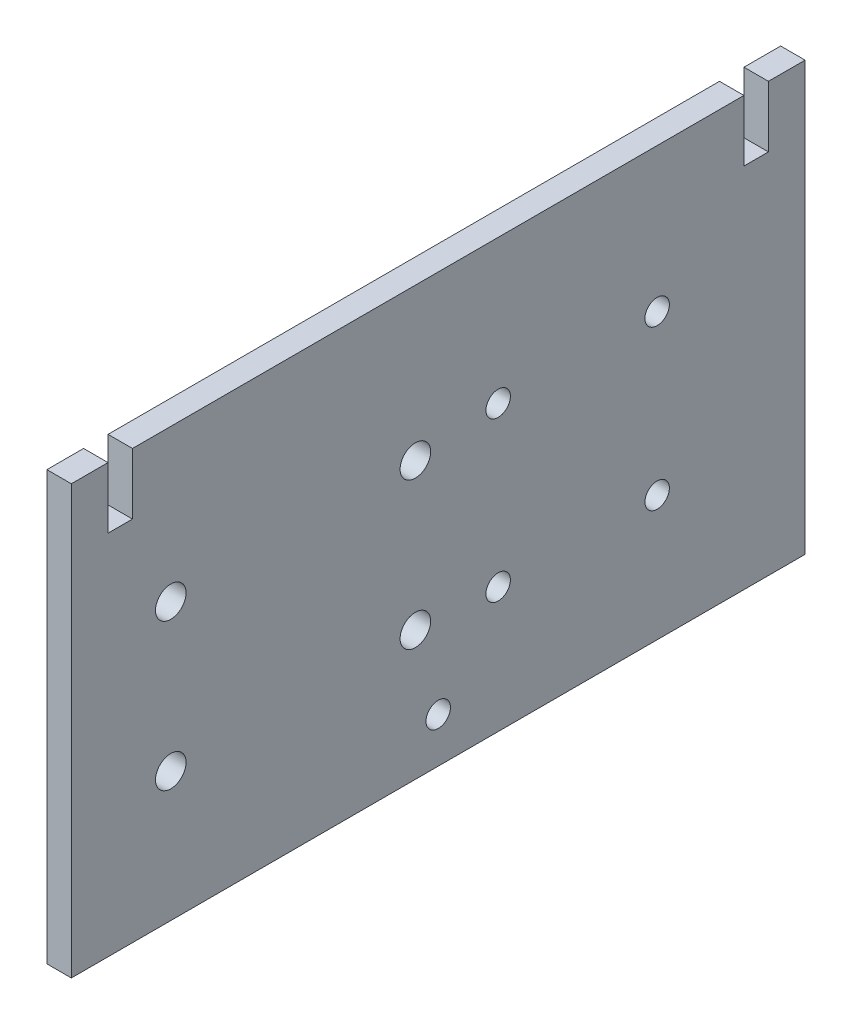
SolidWorks part; units mm, degrees
ref_plane "Спереди" through (0, 0, 0) normal (0, 0, 1) x (1, 0, 0)
ref_plane "Сверху" through (0, 0, 0) normal (0, 1, 0) x (1, 0, 0)
ref_plane "Справа" through (0, 0, 0) normal (1, 0, 0) x (0, 0, -1)
sketch "Эскиз1" plane through (0, 0, 0) normal (1, 0, 0) x (0, 0, -1)
  line L1 (-60, -35) -> (60, -35)
  line L2 (-60, -35) -> (-60, 35)
  line L3 (-60, 35) -> (60, 35)
  line L4 (60, -35) -> (60, 35)
  line L5 (-60, -35) -> (60, 35) construction
  line L6 (-60, 35) -> (60, -35) construction
  point P0 (0, 0)
  dimension "D1" = 70
  dimension "D2" = 120
extrude "Бобышка-Вытянуть1" add sketch "Эскиз1" along normal blind 4
sketch "Эскиз2" plane through (4, 0, 0) normal (1, 0, 0) x (0, 0, -1)
  line L0 (0, 42.6243) -> (50, 42.6243) construction
  line L1 (50, 42.6243) -> (-50, 42.6243) construction
  line L2 (60, 35) -> (-60, 35) construction
  line L3 (-50, 35) -> (-54, 35)
  line L4 (-50, 35) -> (-50, 25)
  line L5 (-50, 25) -> (-54, 25)
  line L6 (-54, 35) -> (-54, 25)
  line L8 (50, 35) -> (54, 35)
  line L9 (50, 35) -> (50, 25)
  line L10 (50, 25) -> (54, 25)
  line L11 (54, 35) -> (54, 25)
  circle A0 centre (0, -27.6605) radius 2
  dimension "D7" = 4
  dimension "D1" = 50
  dimension "D2" = 100
  dimension "D3" = 10
  dimension "D4" = 4
  dimension "D5" = 10
  dimension "D6" = 4
extrude "Вырез-Вытянуть1" cut sketch "Эскиз2" against normal through all
sketch "Эскиз3" plane through (4, 0, 0) normal (1, 0, 0) x (0, 0, -1)
  circle A0 centre (-43.7375, 10.1722) radius 2.5
  circle A1 centre (-43.7375, -13.8278) radius 2.5
  circle A2 centre (-3.7375, -13.8278) radius 2.5
  circle A3 centre (-3.7375, 10.1722) radius 2.5
  circle A4 centre (9.8031, 11.494) radius 2
  circle A5 centre (35.8031, 11.494) radius 2
  circle A6 centre (35.8031, -14.506) radius 2
  circle A7 centre (9.8031, -14.506) radius 2
extrude "Вырез-Вытянуть2" cut sketch "Эскиз3" against normal through all
